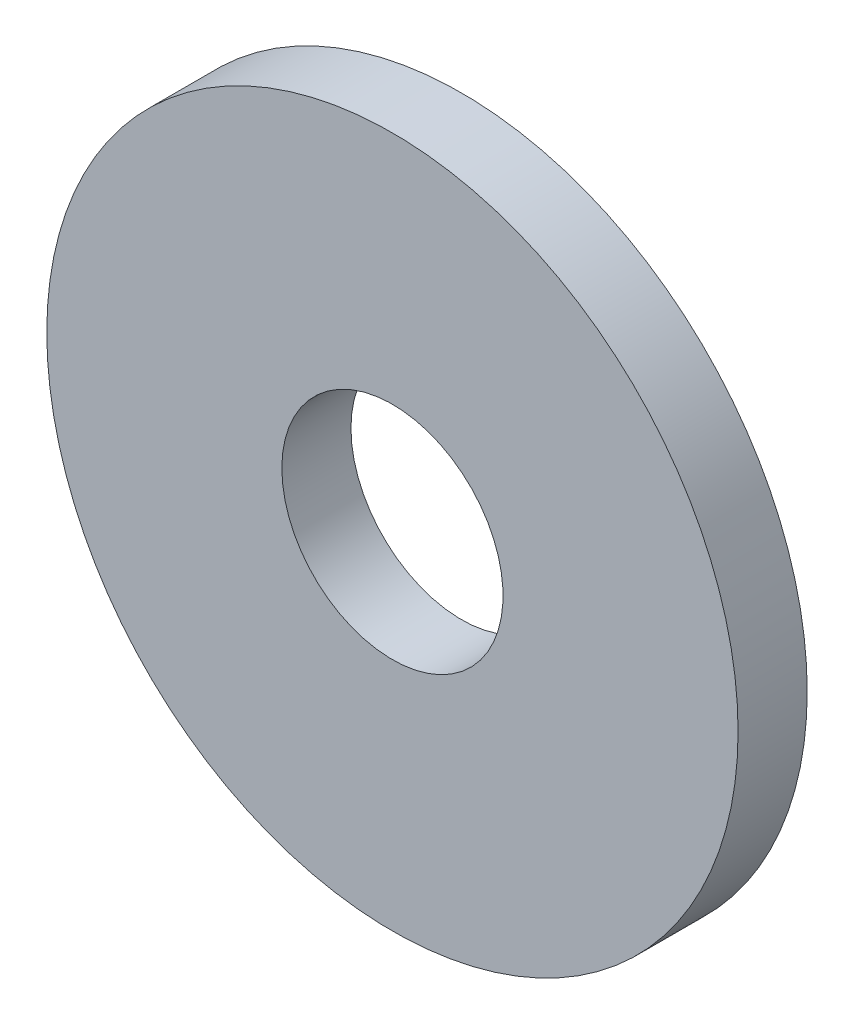
SolidWorks part; units mm, degrees
ref_plane "Front Plane" through (0, 0, 0) normal (0, 0, 1) x (1, 0, 0)
ref_plane "Top Plane" through (0, 0, 0) normal (0, 1, 0) x (1, 0, 0)
ref_plane "Right Plane" through (0, 0, 0) normal (1, 0, 0) x (0, 0, -1)
ref_plane "Plane1" through (0, 0, 0) normal (0, -1, 0) x (1, 0, 0)
sketch "Sketch1" plane through (0, 0, 0) normal (0, -1, 0) x (1, 0, 0)
  line L0 (1.6, 0) -> (5, 0)
  line L1 (5, 0) -> (5, 1)
  line L2 (5, 1) -> (1.6, 1)
  line L3 (1.6, 1) -> (1.6, 0)
  line L4 (0, 1) -> (0, 0) construction
revolve "Revolve1" add sketch "Sketch1" angle 360 about L4
